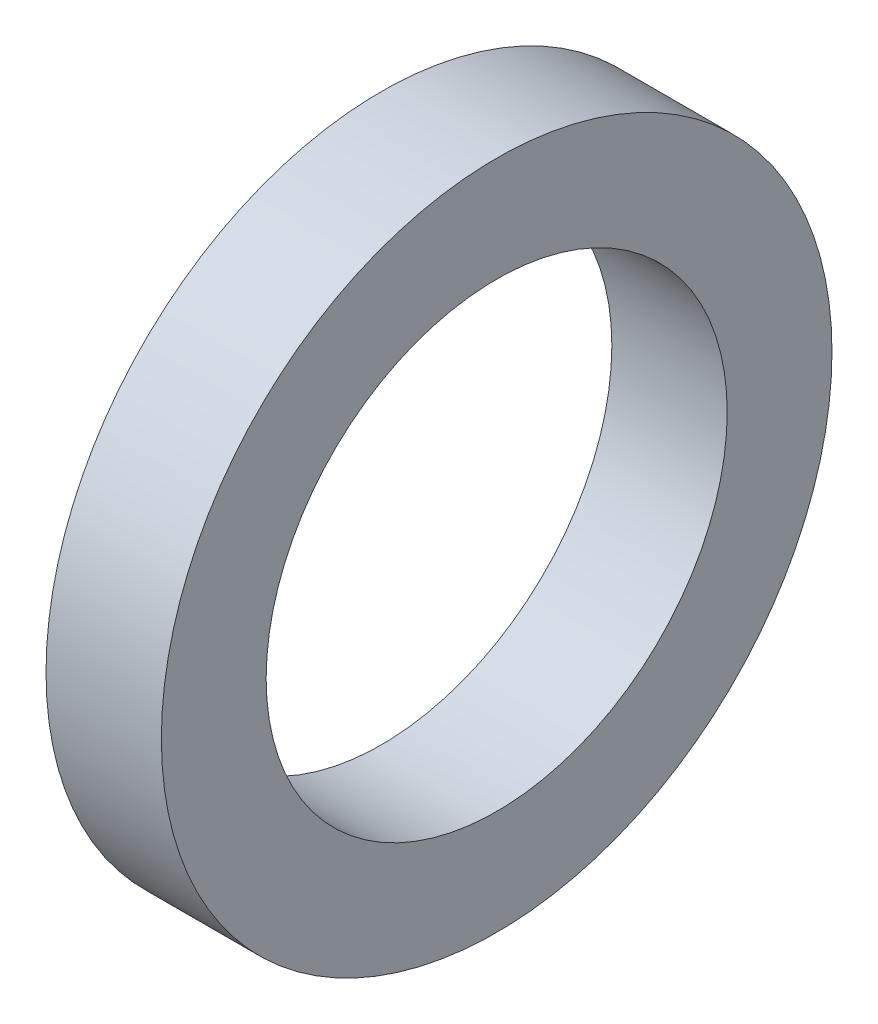
SolidWorks part; units mm, degrees
material "Rubber"
ref_plane "Front Plane" through (0, 0, 0) normal (0, 0, 1) x (1, 0, 0)
ref_plane "Top Plane" through (0, 0, 0) normal (0, 1, 0) x (1, 0, 0)
ref_plane "Right Plane" through (0, 0, 0) normal (1, 0, 0) x (0, 0, -1)
sketch "Sketch1" plane through (0, 0, 0) normal (1, 0, 0) x (0, 0, -1)
  circle A0 centre (0, 0) radius 25.4
  dimension "D1" = 50.8
extrude "Boss-Extrude1" add sketch "Sketch1" along normal blind 8.7376
sketch "Sketch2" plane through (8.7376, 0, 0) normal (1, 0, 0) x (0, 0, -1)
  point P0 (0, 0)
hole_wizard "#97 (1.375) Diameter Hole1" positions "Sketch2" profile "Sketch3" hole size "#97" standard "ANSI Inch" end condition through all
sketch "Sketch3" plane through (8.7376, 0, 0) normal (0, 1, 0) x (0, 0, -1)
  line L0 (0, 0) -> (0, 8.7376)
  line L1 (0, 8.7376) -> (17.4625, 8.7376)
  line L2 (17.4625, 8.7376) -> (17.4625, 0)
  line L5 (17.4625, 0) -> (0, 0)
  line L11 (0, -6.35) -> (0, 107.95) construction
  dimension "Thru Hole Dia." = 34.925
  dimension "Thru Hole Depth" = 8.7376
